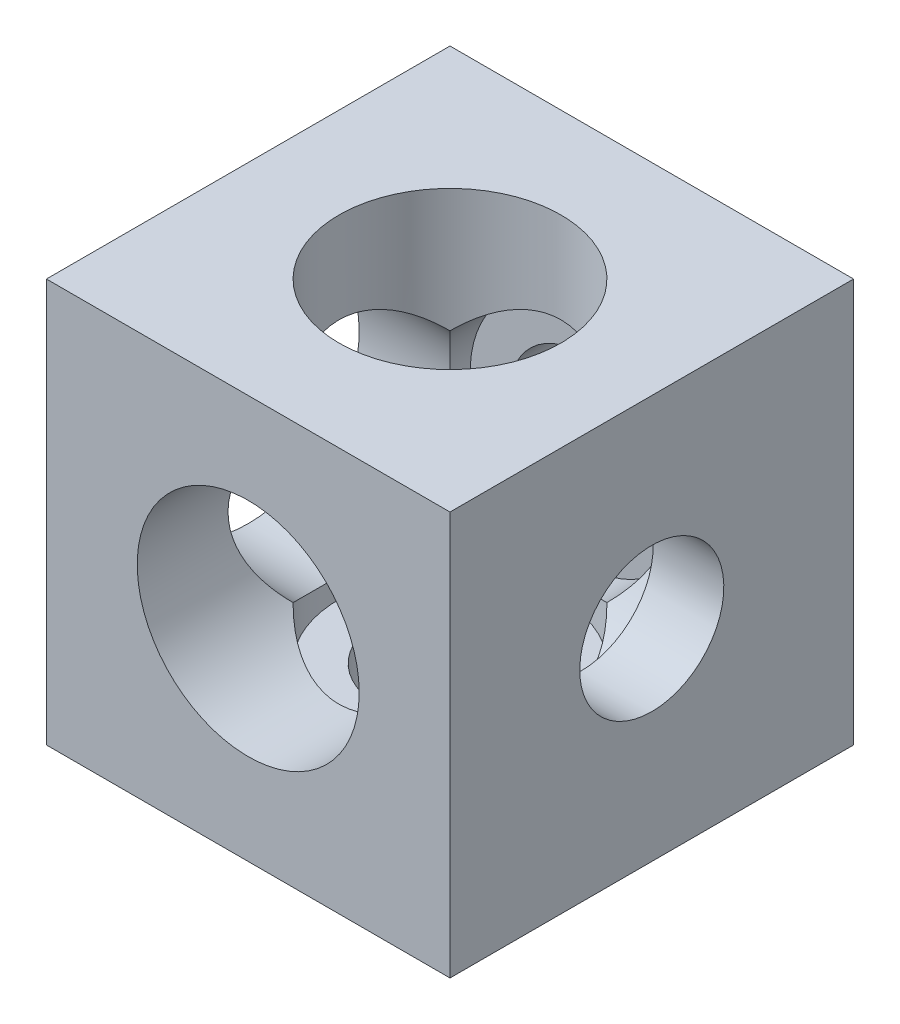
SolidWorks part; units mm, degrees
ref_plane "Front Plane" through (0, 0, 0) normal (0, 0, 1) x (1, 0, 0)
ref_plane "Top Plane" through (0, 0, 0) normal (0, 1, 0) x (1, 0, 0)
ref_plane "Right Plane" through (0, 0, 0) normal (1, 0, 0) x (0, 0, -1)
sketch "Sketch1" plane through (0, 0, 0) normal (0, 0, 1) x (1, 0, 0)
  line L1 (-10, 10) -> (10, 10)
  line L2 (-10, 10) -> (-10, -10)
  line L3 (-10, -10) -> (10, -10)
  line L4 (10, 10) -> (10, -10)
  line L5 (-10, 10) -> (10, -10) construction
  line L6 (-10, -10) -> (10, 10) construction
  point P0 (0, 0)
  dimension "D1" = 20
  dimension "D2" = 20
extrude "Boss-Extrude1" add sketch "Sketch1" along normal mid plane 20
sketch "Sketch2" plane through (0, 0, 10) normal (0, 0, 1) x (1, 0, 0)
  circle A0 centre (0, 0) radius 3.57
  dimension "D1" = 7.14
extrude "Cut-Extrude1" cut sketch "Sketch2" against normal through all
sketch "Sketch3" plane through (0, 0, 10) normal (0, 0, 1) x (1, 0, 0)
  circle A0 centre (0, 0) radius 5.5
  dimension "D1" = 11
extrude "Cut-Extrude2" cut sketch "Sketch3" against normal offset from surface (16.5 mm away) 3.5 up to face at (3.57, 0, -10)
sketch "Sketch4" plane through (-10, 0, 0) normal (-1, 0, 0) x (0, 0, 1)
  circle A0 centre (0, 0) radius 3.57
  dimension "D1" = 7.14
extrude "Cut-Extrude3" cut sketch "Sketch4" against normal through all
sketch "Sketch5" plane through (-10, 0, 0) normal (-1, 0, 0) x (0, 0, 1)
  circle A0 centre (0, 0) radius 5.5
  dimension "D1" = 11
extrude "Cut-Extrude4" cut sketch "Sketch5" against normal offset from surface (16.5 mm away) 3.5 up to face at (10, -3.57, 0)
sketch "Sketch6" plane through (0, 10, 0) normal (0, 1, 0) x (1, 0, 0)
  circle A0 centre (0, 0) radius 3.57
  dimension "D1" = 7.14
extrude "Cut-Extrude5" cut sketch "Sketch6" against normal through all
sketch "Sketch7" plane through (0, 10, 0) normal (0, 1, 0) x (1, 0, 0)
  circle A0 centre (0, 0) radius 5.5
  dimension "D1" = 11
extrude "Cut-Extrude6" cut sketch "Sketch7" against normal offset from surface (16.5 mm away) 3.5 up to face at (0, -10, 3.57)
